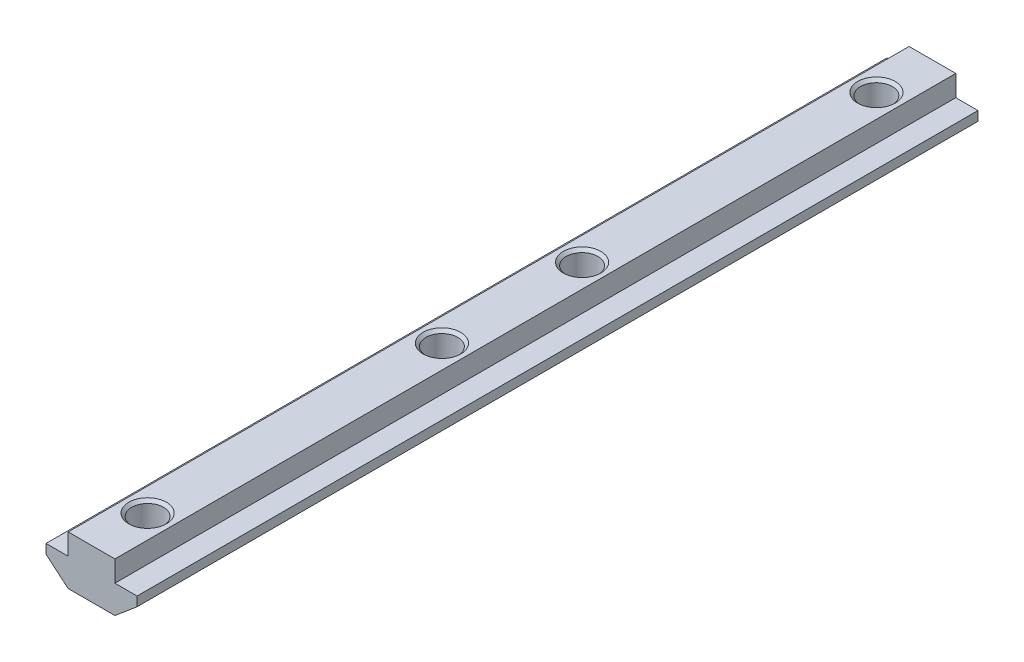
SolidWorks part; units mm, degrees
ref_plane "Спереди" through (0, 0, 0) normal (0, 0, 1) x (1, 0, 0)
ref_plane "Сверху" through (0, 0, 0) normal (0, 1, 0) x (1, 0, 0)
ref_plane "Справа" through (0, 0, 0) normal (1, 0, 0) x (0, 0, -1)
sketch "Эскиз1" plane through (0, 0, 0) normal (0, 0, 1) x (1, 0, 0)
  line L0 (5, 0) -> (-5, 0)
  line L1 (-5, 0) -> (-5, -4.5)
  line L2 (-5, -4.5) -> (-9.75, -4.5)
  line L3 (-9.75, -4.5) -> (-9.75, -6.5)
  line L4 (-9.75, -6.5) -> (-5, -10.5)
  line L5 (-5, -10.5) -> (5, -10.5)
  line L6 (0, -10.5) -> (0, 0) construction
  line L7 (9.75, -6.5) -> (5, -10.5)
  line L8 (9.75, -4.5) -> (9.75, -6.5)
  line L9 (5, -4.5) -> (9.75, -4.5)
  line L10 (5, 0) -> (5, -4.5)
  dimension "D1" = 10
  dimension "D2" = 19.5
  dimension "D3" = 10.5
  dimension "D4" = 6
  dimension "D5" = 2
extrude "Бобышка-Вытянуть1" add sketch "Эскиз1" along normal mid plane 180
hole_wizard "Отверстие обработанное метчиком M81" positions "Эскиз7" profile "Эскиз8" tap size "M8" standard "ISO" end condition through all
sketch "Эскиз7" plane through (0, 0, 0) normal (0, 1, 0) x (1, 0, 0)
  line L0 (0, 90) -> (0, 78)
  line L1 (5, 90) -> (-5, 90) construction
  line L2 (0, 78) -> (0, 15)
  line L4 (0, -15) -> (0, -78)
  line L5 (0, -78) -> (0, -90)
  line L6 (5, -90) -> (-5, -90) construction
  point P0 (0, 78)
  point P2 (0, 15)
  point P4 (0, -15)
  point P6 (0, -78)
  dimension "D1" = 30
  dimension "D2" = 156
sketch "Эскиз8" plane through (0, 0, -78) normal (1, 0, 0) x (0, 0, 1)
  line L0 (0, 0) -> (0, 10.5)
  line L1 (0, 10.5) -> (4.025, 10.5)
  line L2 (3.4, 9.875) -> (3.4, 0.625)
  line L3 (3.4, 0.625) -> (4.025, 0)
  line L5 (4.025, 0) -> (0, 0)
  line L6 (-3.4, 0.625) -> (-4.025, 0) construction
  line L7 (4.025, 10.5) -> (3.4, 9.875)
  line L8 (-4.025, 10.5) -> (-3.4, 9.875) construction
  line L11 (0, -6.35) -> (0, 107.95) construction
  dimension "Диаметр проходного сверла" = 6.8
  dimension "Глубина проходного сверла" = 10.5
  dimension "Диаметр передней зенковки" = 8.05
  dimension "Угол передней зенковки" = 90
  dimension "Диаметр задней зенковки" = 8.05
  dimension "Угол задней зенковки" = 90
cosmetic thread "Отверстие резьбы9" parameters "D2"=8
cosmetic thread "Отверстие резьбы10" parameters "D2"=8
cosmetic thread "Отверстие резьбы11" parameters "D2"=8
cosmetic thread "Отверстие резьбы12" parameters "D2"=8
